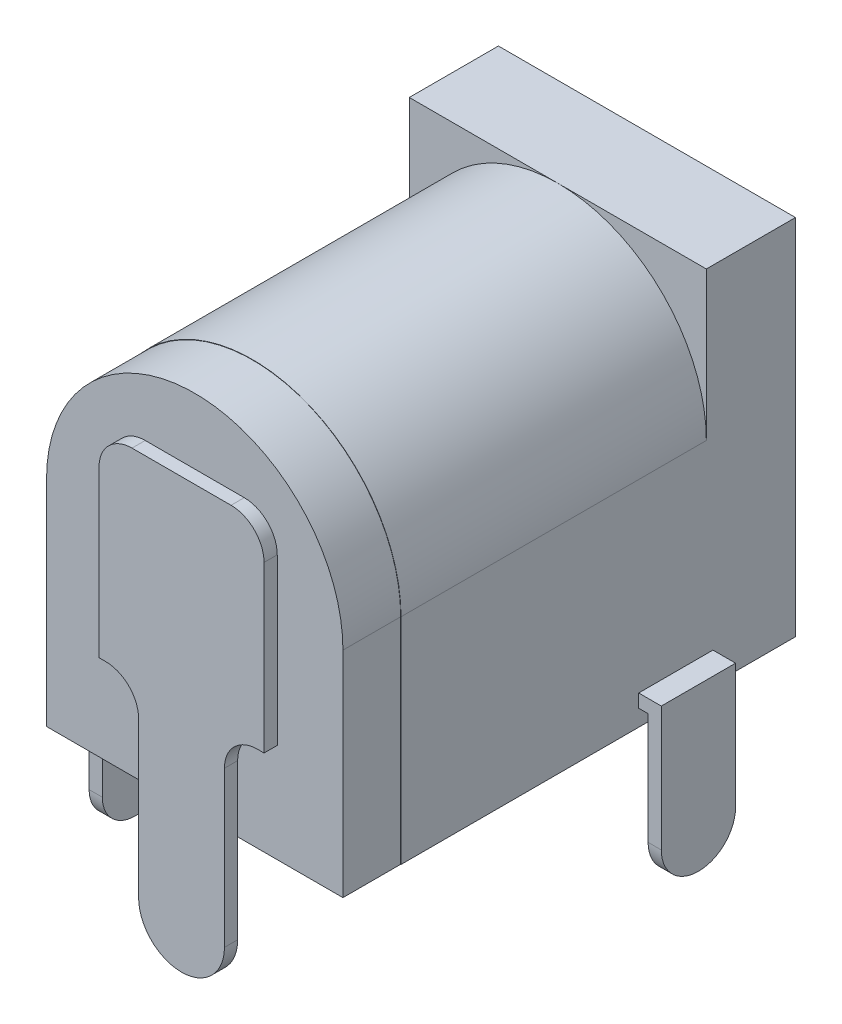
SolidWorks part; units mm, degrees
ref_plane "Plan de face" through (0, 0, 0) normal (0, 0, 1) x (1, 0, 0)
ref_plane "Plan de dessus" through (0, 0, 0) normal (0, 1, 0) x (1, 0, 0)
ref_plane "Plan de droite" through (0, 0, 0) normal (1, 0, 0) x (0, 0, -1)
sketch "Esquisse1" plane through (0, 0, 0) normal (0, 0, 1) x (1, 0, 0)
  line L0 (0, -6.0433) -> (0, 37.3263) construction
  line L1 (-10.0722, 0) -> (24.4251, 0) construction
  line L2 (-4.5, 11.8416) -> (-4.5, -3.2796) construction
  line L3 (-2.0077, 6.5) -> (2.0892, 6.5) construction
  line L4 (-11.6663, 11) -> (1.9154, 11) construction
  line L5 (4.5, -1.9139) -> (4.5, 13.9273) construction
  line L6 (4.5, 6.5) -> (4.5, 0)
  line L7 (4.5, 0) -> (-4.5, 0)
  line L8 (-4.5, 0) -> (-4.5, 6.5)
  arc A0 (4.5, 6.5) -> (-4.5, 6.5) centre (0, 6.5) ccw
  dimension "D1" = 11
  dimension "D2" = 4.5
  dimension "D3" = 4.5
  dimension "D4" = 4.5
extrude "Extrusion1" add sketch "Esquisse1" along normal blind 9.25
sketch "Esquisse2" plane through (0, 0, 9.25) normal (0, 0, 1) x (1, 0, 0)
  line L0 (-6.0566, 0) -> (5.9794, 0) construction
  line L1 (4.49, 6.4943) -> (4.49, 0)
  line L2 (4.48, -1.3487) -> (4.4971, 12.0589) construction
  line L3 (4.49, 0) -> (-4.49, 0)
  line L4 (5.2397, 11) -> (-6.0566, 11) construction
  line L5 (-4.49, 0) -> (-4.49, 6.5)
  line L6 (-4.4835, 11.7885) -> (-4.5, -1.6772) construction
  line L7 (0, -1.6772) -> (0, 12.5999) construction
  line L8 (-2.9076, 6.5) -> (1.8836, 6.5) construction
  arc A0 (4.49, 6.4943) -> (-4.49, 6.5) centre (0, 6.5) ccw
extrude "Extrusion2" add sketch "Esquisse2" along normal blind 1.75
sketch "Esquisse3" plane through (0, 0, 0) normal (0, 0, -1) x (-1, 0, 0)
  line L0 (-5.11, 0) -> (6.3658, 0) construction
  line L1 (-4.5, -0.5566) -> (-4.5, 12.1942) construction
  line L2 (-5.3805, 11) -> (6.7328, 11) construction
  line L3 (4.5, -0.7692) -> (4.5, 11.8851) construction
  line L5 (-4.5, 11) -> (4.5, 11)
  line L6 (-4.5, 11) -> (-4.5, 0)
  line L7 (-4.5, 0) -> (4.5, 0)
  line L8 (4.5, 11) -> (4.5, 0)
extrude "Extrusion3" add sketch "Esquisse3" along normal blind 2.7
sketch "Esquisse5" plane through (0, 0, -2.7) normal (0, 0, -1) x (-1, 0, 0)
  line L0 (0, -1.258) -> (0, 10.1946) construction
  line L1 (-3.3036, 6.5) -> (2.3299, 6.5) construction
  circle A0 centre (0, 6.5) radius 3.1
extrude "Enlèv. mat.-Extru.1" cut sketch "Esquisse5" against normal blind 10
sketch "Esquisse6" plane through (0, 0, 7.3) normal (0, 0, -1) x (-1, 0, 0)
  line L0 (0, 2.9064) -> (0, 8.7198) construction
  line L1 (-0.816, 6.5) -> (1.8351, 6.5) construction
  circle A0 centre (0, 6.5) radius 1
extrude "Extrusion4" add sketch "Esquisse6" along normal blind 8
fillet "Congé1" radius 0.99 1 edges at (-1, 6.5, -0.7)
sketch "Esquisse7" plane through (0, 0, 11) normal (0, 0, 1) x (1, 0, 0)
  line L0 (0, -9.1727) -> (0, 13.5797) construction
  line L1 (-1.4786, 6.5) -> (3.0378, 6.5) construction
  line L2 (-2.5, 12.2746) -> (-2.5, -1.2249) construction
  line L3 (2.5, 12.2746) -> (2.5, -1.2249) construction
  line L4 (-1.3, 4.5898) -> (-1.3, -9.1727) construction
  line L5 (-5.8045, 9) -> (8.4254, 9) construction
  line L6 (-3.3501, 3) -> (-0.4866, 3) construction
  line L7 (-5.1909, -4) -> (7.5781, -4) construction
  line L8 (-6.7103, 0) -> (7.1398, 0) construction
  line L9 (1.5, 9) -> (-1.5, 9)
  line L10 (-2.5, 8) -> (-2.5, 3)
  line L11 (-2.5, 3) -> (-2.3, 3)
  line L12 (-1.3, 2) -> (-1.3, -2.7)
  line L13 (0.6915, -2.7) -> (-2.3, -2.7) construction
  line L14 (1.3, 2) -> (1.3, -2.7)
  line L15 (2.5, 3) -> (2.3, 3)
  line L16 (2.5, 8) -> (2.5, 3)
  arc A0 (-1.5, 9) -> (-2.5, 8) centre (-1.5, 8) ccw
  arc A1 (-2.3, 3) -> (-1.3, 2) centre (-2.3, 2) cw
  arc A2 (-1.3, -2.7) -> (1.3, -2.7) centre (0, -2.7) ccw
  arc A3 (2.3, 3) -> (1.3, 2) centre (2.3, 2) ccw
  arc A4 (1.5, 9) -> (2.5, 8) centre (1.5, 8) cw
  point P38 (0, 9)
  dimension "D7" = 1
  dimension "D8" = 1.3
  dimension "D1" = 2.5
  dimension "D2" = 2.5
  dimension "D3" = 4
  dimension "D4" = 9
  dimension "D5" = 6
  dimension "D6" = 1.3
extrude "Extrusion5" add sketch "Esquisse7" along normal blind 0.4
sketch "Esquisse8" plane through (4.5, 0, 0) normal (1, 0, 0) x (0, 0, -1)
  line L0 (-10.5, -5.9247) -> (-10.5, 12.8028) construction
  line L1 (-0.8, -5.9247) -> (-0.8, 2.3661) construction
  line L2 (-9.4524, -4) -> (5.5198, -4) construction
  line L3 (3.2764, 0.5) -> (-3.405, 0.5) construction
  line L4 (5.3168, 0.9) -> (-3.405, 0.9) construction
  line L5 (0.2, -1.0965) -> (0.2, 2.6344) construction
  line L6 (-2.05, -1.0965) -> (-2.05, 2.3661) construction
  line L7 (3.133, 0) -> (4.7289, 0) construction
  line L8 (5.3168, 0.7) -> (-1.705, 0.7) construction
  line L9 (-2.05, 0.9) -> (0.2, 0.9)
  line L10 (-2.05, 0.9) -> (-2.05, 0.5)
  line L11 (-2.05, 0.5) -> (0.2, 0.5)
  line L12 (0.2, 0.9) -> (0.2, 0.5)
  dimension "D1" = 9.7
  dimension "D2" = 1.25
  dimension "D3" = 2.25
  dimension "D4" = 0.5
  dimension "D5" = 0.4
  dimension "D6" = 0.2
ref_plane "Plan1" through (0, 0, 0.8) normal (0, 0, 1) x (1, 0, 0)
sketch "Esquisse9" plane through (0, 0, 0.8) normal (0, 0, 1) x (1, 0, 0)
  line L0 (4.5, -9.0621) -> (4.5, 15.3025) construction
  line L1 (5, 1.8803) -> (5, -8.4324) construction
  line L2 (1.0558, -4) -> (7.9046, -4) construction
  line L3 (4.5, 0.7145) -> (8.888, 0.7145) construction
  line L4 (4.5, 0.7145) -> (5, 0.7145)
  line L5 (5, 0.7145) -> (5, -4)
  dimension "D1" = 0.5
sweep "Balayage1" add profiles "Esquisse8" path "Esquisse9"
fillet "Congé2" radius 1.124 2 edges at (4.9855, -4, -0.2) (4.9855, -4, 2.05)
sketch "Esquisse10" plane through (-4.5, 0, 0) normal (-1, 0, 0) x (0, 0, 1)
  line L0 (12.4001, 0) -> (-6.8868, 0) construction
  line L1 (12.4001, 4.6) -> (-0.638, 4.6) construction
  line L2 (11.3406, 4.8) -> (5.027, 4.8) construction
  line L3 (11.5569, 5) -> (4.5729, 5) construction
  line L4 (9, 2.0751) -> (9, 5.2752) construction
  line L5 (7, 5.2752) -> (7, 2.0751) construction
  line L6 (10.5, -5.7305) -> (10.5, -2.7) construction
  line L7 (8, 5.1454) -> (8, -5.7305) construction
  line L9 (7, 5) -> (9, 5)
  line L10 (7, 5) -> (7, 4.6)
  line L11 (7, 4.6) -> (9, 4.6)
  line L12 (9, 5) -> (9, 4.6)
  dimension "D1" = 2.5
  dimension "D2" = 5
  dimension "D3" = 0.2
  dimension "D4" = 0.2
  dimension "D5" = 1
  dimension "D6" = 1
ref_plane "Plan2" through (0, 0, 8) normal (0, 0, 1) x (1, 0, 0)
sketch "Esquisse11" plane through (0, 0, 8) normal (0, 0, 1) x (1, 0, 0)
  line L0 (4.456, -4) -> (-6.8901, -4) construction
  line L1 (-5, -4.7028) -> (-5, 6.1845) construction
  line L2 (-4.5, 4.8) -> (-5.8461, 4.8) construction
  line L3 (-4.5, 4.8) -> (-5, 4.8)
  line L4 (-5, 4.8) -> (-5, -4)
  line L5 (-4.5, -8.6321) -> (-4.5, 15.6475) construction
  dimension "D1" = 0.5
sweep "Balayage2" add profiles "Esquisse10" path "Esquisse11"
fillet "Congé3" radius 0.99 2 edges at (-5, -4, 7) (-5, -4, 9)
